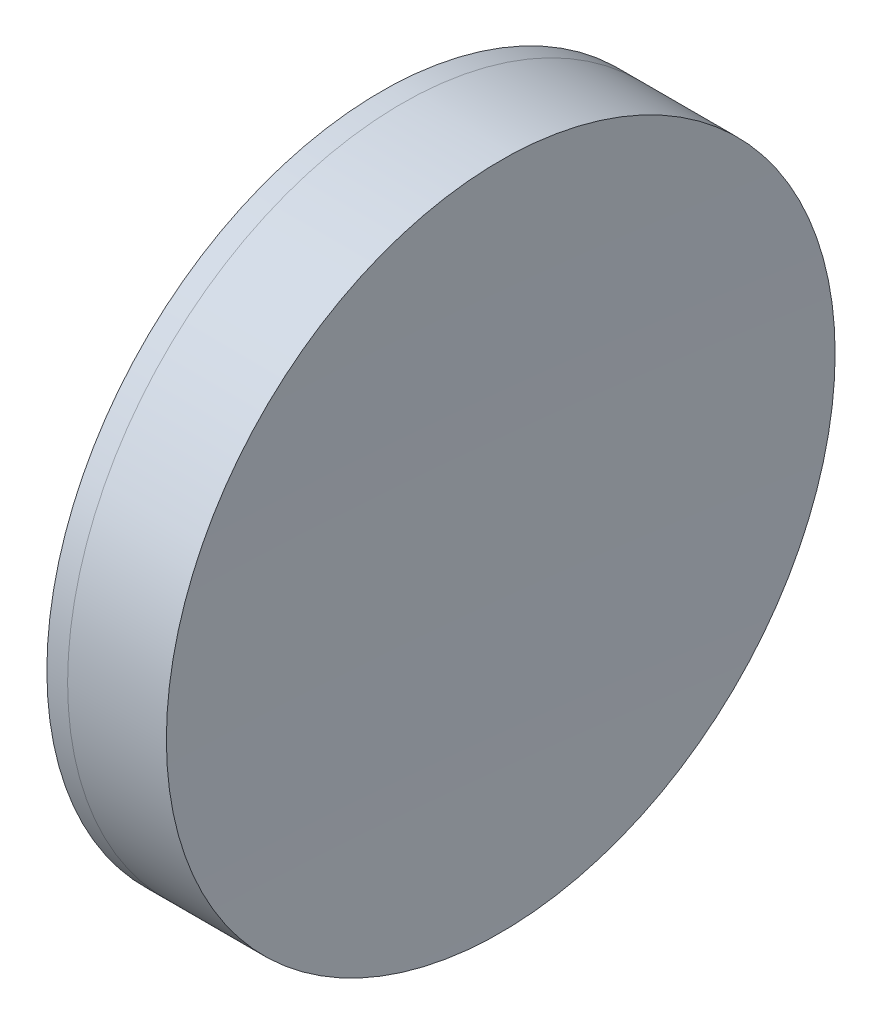
SolidWorks part; units mm, degrees
ref_plane "前视基准面" through (0, 0, 0) normal (0, 0, 1) x (1, 0, 0)
ref_plane "上视基准面" through (0, 0, 0) normal (0, 1, 0) x (1, 0, 0)
ref_plane "右视基准面" through (0, 0, 0) normal (1, 0, 0) x (0, 0, -1)
sketch "草图1" plane through (0, 0, 0) normal (0, 1, 0) x (1, 0, 0)
  line L0 (124.5233, 0) -> (646.9917, 0) construction
  line L1 (302.5086, -12.7) -> (303.2964, -12.7)
  line L2 (302.5086, 12.7) -> (303.2964, 12.7)
  arc A0 (303.2964, -12.7) -> (303.2964, 12.7) centre (263.0843, 0) ccw
  arc A1 (302.5086, 12.7) -> (302.5086, -12.7) centre (337.1543, 0) ccw
  point P10 (300.2543, 0)
  point P11 (305.2543, 0)
  dimension "D3" = 36.9
  dimension "D4" = 42.17
  dimension "D1" = 12.7
  dimension "D2" = 12.7
  dimension "D5" = 5
revolve "旋转1" add sketch "草图1" angle 360 about L0
sketch "草图2" plane through (0, 0, 0) normal (0, 1, 0) x (1, 0, 0)
  line L0 (-0.5519, 0) -> (622.6607, 0) construction
  line L2 (303.2964, 12.7) -> (307.0473, 12.7)
  line L3 (303.2964, -12.7) -> (307.0473, -12.7)
  arc A0 (307.0473, 12.7) -> (307.0473, -12.7) centre (724.6543, 0) ccw
  arc A1 (303.2964, -12.7) -> (303.2964, 12.7) centre (263.0843, 0) ccw construction
  arc A2 (303.2964, -12.7) -> (303.2964, 12.7) centre (263.0843, 0) ccw
  point P8 (306.8543, 0)
  point P12 (305.2543, 0)
  dimension "D1" = 417.8
  dimension "D2" = 1.6
revolve "旋转3" add sketch "草图2" angle 360 about L0
